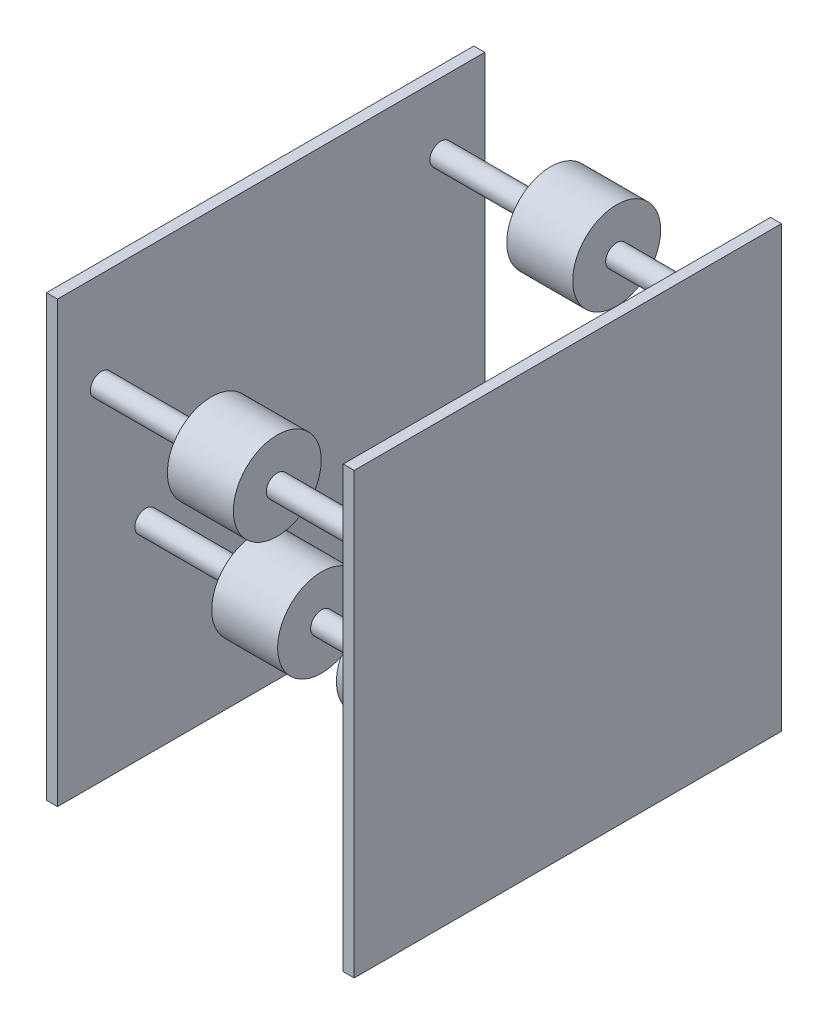
SolidWorks part; units mm, degrees
ref_plane "Front Plane" through (0, 0, 0) normal (0, 0, 1) x (1, 0, 0)
ref_plane "Top Plane" through (0, 0, 0) normal (0, 1, 0) x (1, 0, 0)
ref_plane "Right Plane" through (0, 0, 0) normal (1, 0, 0) x (0, 0, -1)
sketch "Sketch1" plane through (0, 0, 0) normal (1, 0, 0) x (0, 0, -1)
  line L0 (221.5009, 215.9) -> (221.5009, 19.05) construction
  line L1 (0, 0) -> (246.9009, 0)
  line L2 (0, 0) -> (0, 254)
  line L3 (0, 254) -> (246.9009, 254)
  line L4 (246.9009, 0) -> (246.9009, 254)
  line L5 (221.5009, 215.9) -> (25.4, 198.7434) construction
  line L6 (221.5009, 215.9) -> (123.0759, 45.4229) construction
  line L7 (221.5009, 215.9) -> (51.0238, 117.475) construction
  circle A0 centre (221.5009, 215.9) radius 25.4 construction
  circle A1 centre (25.4, 198.7434) radius 25.4 construction
  circle A2 centre (51.0238, 117.475) radius 25.4 construction
  circle A3 centre (123.0759, 45.4229) radius 25.4 construction
  circle A4 centre (221.5009, 19.05) radius 25.4 construction
  arc A5 (25.4, 198.7434) -> (221.5009, 19.05) centre (221.5009, 215.9) ccw construction
  circle A6 centre (-271.9525, -27.6685) radius 76.2 construction
  point P4 (-271.9525, -27.6685)
  point P7 (246.8526, 62.6715)
  dimension "D1" = 50.8
  dimension "D2" = 50.8
  dimension "D3" = 146.05
  dimension "D4" = 30
  dimension "D9" = 38.1
  dimension "D10" = 152.4
  dimension "D5" = 30
  dimension "D6" = 25.4
  dimension "D7" = 25.4
  dimension "D8" = 25
  dimension "D11" = 254
extrude "Boss-Extrude1" add sketch "Sketch1" along normal mid plane 177.8
sketch "Sketch2" plane through (0, 254, 0) normal (0, 1, 0) x (1, 0, 0)
  line L0 (88.9, 0) -> (-88.9, 0) construction
  line L1 (88.9, 246.9009) -> (-88.9, 246.9009) construction
  line L2 (-82.55, 0) -> (82.55, 0)
  line L3 (-82.55, 0) -> (-82.55, 246.9009)
  line L4 (-82.55, 246.9009) -> (82.55, 246.9009)
  line L5 (82.55, 0) -> (82.55, 246.9009)
  line L6 (-88.9, 246.9009) -> (-88.9, 0) construction
  line L7 (88.9, 246.9009) -> (88.9, 0) construction
  dimension "D1" = 6.35
  dimension "D2" = 6.35
extrude "Cut-Extrude1" cut sketch "Sketch2" against normal through all both and the other way through all
sketch "Sketch3" plane through (0, 0, 0) normal (1, 0, 0) x (0, 0, -1)
  circle A0 centre (221.5009, 215.9) radius 25.4 construction
  circle A1 centre (25.4, 198.7434) radius 25.4 construction
  circle A2 centre (221.5009, 19.05) radius 25.4 construction
  circle A3 centre (123.0759, 45.4229) radius 25.4 construction
  circle A4 centre (51.0238, 117.475) radius 25.4 construction
  circle A5 centre (221.5009, 215.9) radius 25.4
  circle A6 centre (25.4, 198.7434) radius 25.4
  circle A7 centre (221.5009, 19.05) radius 25.4
  circle A8 centre (123.0759, 45.4229) radius 25.4
  circle A9 centre (51.0238, 117.475) radius 25.4
extrude "Boss-Extrude2" add sketch "Sketch3" along normal mid plane 38.1 separate body
sketch "Sketch4" plane through (0, 0, 0) normal (1, 0, 0) x (0, 0, -1)
  circle A0 centre (221.5009, 19.05) radius 6.35
  circle A1 centre (123.0759, 45.4229) radius 6.35
  circle A2 centre (51.0238, 117.475) radius 6.35
  circle A3 centre (25.4, 198.7434) radius 6.35
  circle A4 centre (221.5009, 215.9) radius 6.35
  dimension "D1" = 12.7
extrude "Boss-Extrude3" add sketch "Sketch4" along normal up to surface and the other way up to surface
sketch "Sketch5" plane through (0, 0, 0) normal (0, -1, 0) x (1, 0, 0)
  line L0 (-88.9, 0) -> (-88.9, -246.9009) construction
  line L1 (88.9, 0) -> (88.9, -246.9009) construction
  circle A0 centre (0, -123.4505) radius 88.9 construction
  point P6 (0, 0)
  point P7 (0, -160.465)
  point P8 (88.9, -123.4505)
